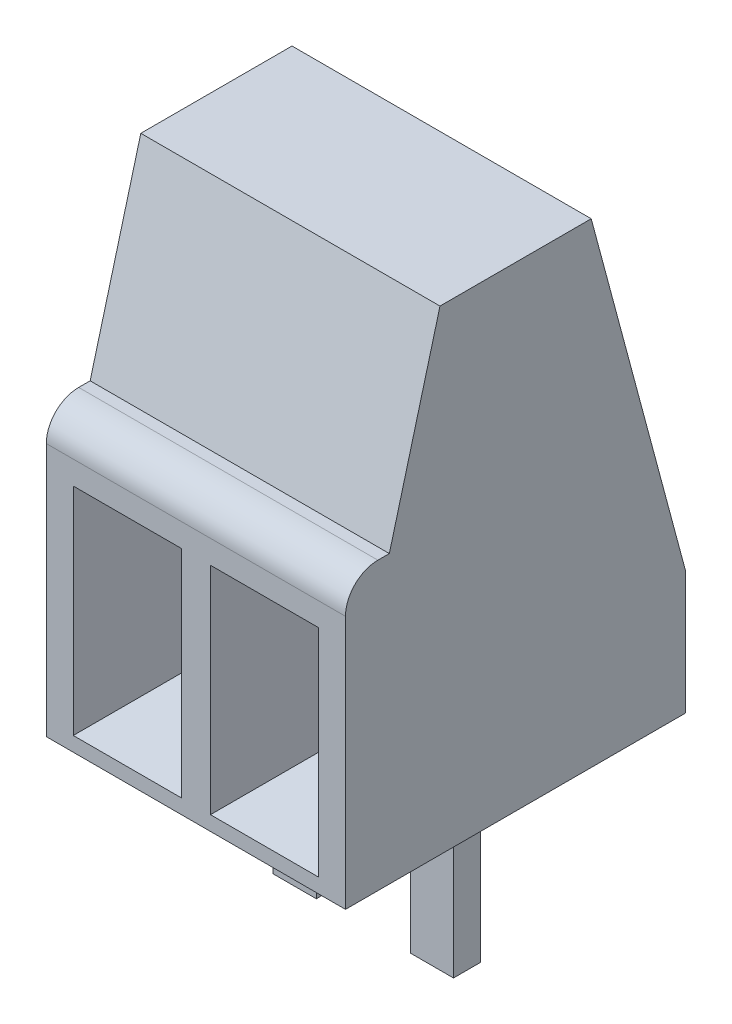
SolidWorks part; units mm, degrees
ref_plane "Front Plane" through (0, 0, 0) normal (0, 0, 1) x (1, 0, 0)
ref_plane "Top Plane" through (0, 0, 0) normal (0, 1, 0) x (1, 0, 0)
ref_plane "Right Plane" through (0, 0, 0) normal (1, 0, 0) x (0, 0, -1)
sketch "Sketch1" plane through (0, 0, 0) normal (0, 1, 0) x (1, 0, 0)
  line L1 (-2.77, -3.15) -> (2.77, -3.15)
  line L2 (-2.77, -3.15) -> (-2.77, 3.15)
  line L3 (-2.77, 3.15) -> (2.77, 3.15)
  line L4 (2.77, -3.15) -> (2.77, 3.15)
  line L5 (-2.77, -3.15) -> (2.77, 3.15) construction
  line L6 (-2.77, 3.15) -> (2.77, -3.15) construction
  point P0 (0, 0)
  dimension "D1" = 5.54
  dimension "D2" = 6.3
extrude "Boss-Extrude1" add sketch "Sketch1" along normal blind 8.8
sketch "Sketch2" plane through (0, 0, 0) normal (0, 1, 0) x (1, 0, 0)
  line L1 (0.87, -0.05) -> (1.67, -0.05)
  line L2 (0.87, -0.05) -> (0.87, 0.45)
  line L3 (0.87, 0.45) -> (1.67, 0.45)
  line L4 (1.67, -0.05) -> (1.67, 0.45)
  line L5 (0.87, -0.05) -> (1.67, 0.45) construction
  line L6 (0.87, 0.45) -> (1.67, -0.05) construction
  line L11 (2.77, 3.15) -> (-2.77, 3.15) construction
  line L13 (-0.87, -0.05) -> (-1.67, -0.05)
  line L14 (-0.87, -0.05) -> (-0.87, 0.45)
  line L15 (-0.87, 0.45) -> (-1.67, 0.45)
  line L16 (-1.67, -0.05) -> (-1.67, 0.45)
  line L17 (-0.87, -0.05) -> (-1.67, 0.45) construction
  line L18 (-0.87, 0.45) -> (-1.67, -0.05) construction
  point P0 (1.27, 0.2)
  point P11 (-1.27, 0.2)
  point P20 (1.27, 0.2)
  dimension "D1" = 2.54
  dimension "D2" = 0.8
  dimension "D3" = 2.95
  dimension "D4" = 0.5
  dimension "D5" = 1.27
extrude "Boss-Extrude2" add sketch "Sketch2" against normal blind 3.2
sketch "Sketch3" plane through (2.77, 0, 0) normal (1, 0, 0) x (0, 0, -1)
  line L1 (-3.15, 8.8) -> (-3.15, 0) construction
  line L2 (-2.55, 5.3) -> (-2.3378, 5.3)
  line L3 (-2.3378, 5.3) -> (-1.4, 8.8)
  line L4 (-3.15, 8.8) -> (3.15, 8.8) construction
  line L5 (-1.4, 8.8) -> (1.4, 8.8)
  line L6 (1.4, 8.8) -> (3.15, 2.2689)
  line L7 (3.15, 8.8) -> (3.15, 0) construction
  line L10 (1.4, 8.8) -> (3.15, 8.8)
  line L11 (3.15, 8.8) -> (3.15, 2.2689)
  line L12 (-3.15, 4.7) -> (-3.15, 8.8)
  line L13 (-3.15, 8.8) -> (-1.4, 8.8)
  line L14 (-3.15, 0) -> (3.15, 0) construction
  arc A0 (-3.15, 4.7) -> (-2.55, 5.3) centre (-2.55, 4.7) cw
  point P18 (0, 8.8)
  line M12 (3.15, 0) -> (3.15, 8.8)
  line M13 (3.15, 8.8) -> (-3.15, 8.8)
  line M14 (-3.15, 8.8) -> (-3.15, 0)
  dimension "D3" = 4.7
  dimension "D1" = 15
  dimension "D2" = 75
  dimension "D4" = 2.8
  dimension "D5" = 5.3
extrude "Cut-Extrude1" cut sketch "Sketch3" against normal up to next contours A0 L2 L3 M14 M13 | L6 M13 M12
sketch "Sketch4" plane through (0, 0, 3.15) normal (0, 0, 1) x (1, 0, 0)
  line L7 (-2.27, 0.2689) -> (-0.27, 0.2689)
  line L8 (-2.27, 0.2689) -> (-2.27, 4.2689)
  line L9 (-2.27, 4.2689) -> (-0.27, 4.2689)
  line L10 (-0.27, 0.2689) -> (-0.27, 4.2689)
  line L11 (-2.27, 0.2689) -> (-0.27, 4.2689) construction
  line L12 (-2.27, 4.2689) -> (-0.27, 0.2689) construction
  line L13 (2.27, 4.2689) -> (0.27, 4.2689)
  line L14 (2.27, 4.2689) -> (2.27, 0.2689)
  line L15 (2.27, 0.2689) -> (0.27, 0.2689)
  line L16 (0.27, 4.2689) -> (0.27, 0.2689)
  line L17 (2.27, 4.2689) -> (0.27, 0.2689) construction
  line L18 (2.27, 0.2689) -> (0.27, 4.2689) construction
  line L29 (0.87, -3.2) -> (1.67, -3.2) construction
  line L30 (-1.67, -3.2) -> (-0.87, -3.2) construction
  point P5 (-1.27, 2.2689)
  point P10 (1.27, 2.2689)
  point P21 (0, 2.2689)
  point P32 (1.27, -3.2)
  point P35 (-1.27, -3.2)
  dimension "D1" = 2
  dimension "D2" = 4
extrude "Cut-Extrude2" cut sketch "Sketch4" against normal blind 3.15 draft 10
